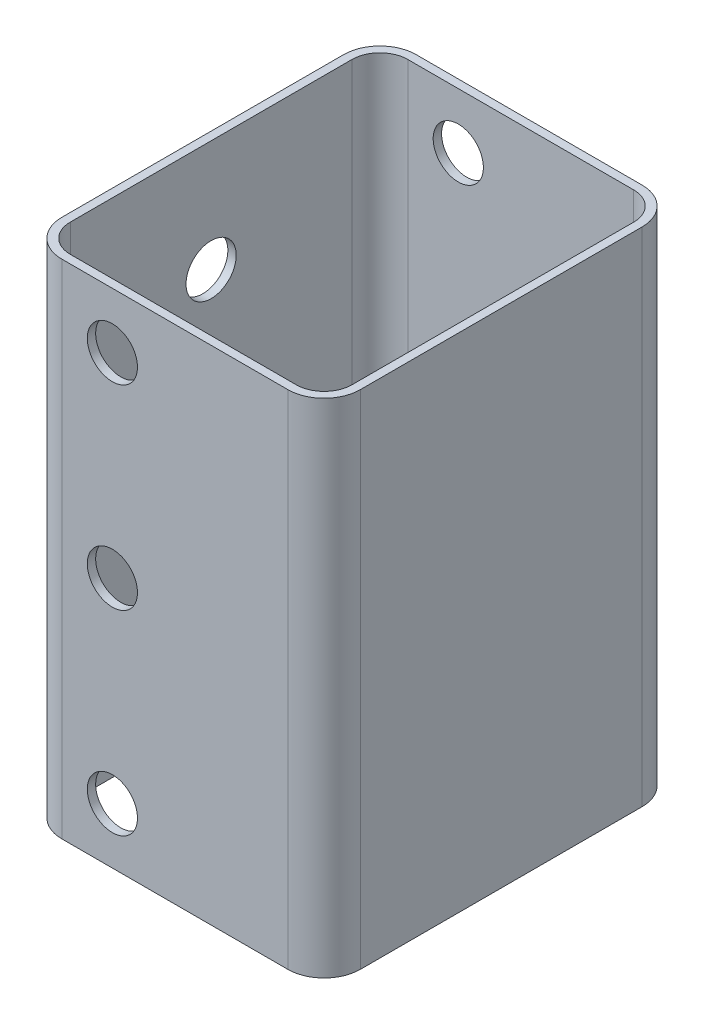
SolidWorks part; units mm, degrees
ref_plane "Front Plane" through (0, 0, 0) normal (0, 0, 1) x (1, 0, 0)
ref_plane "Top Plane" through (0, 0, 0) normal (0, 1, 0) x (1, 0, 0)
ref_plane "Right Plane" through (0, 0, 0) normal (1, 0, 0) x (0, 0, -1)
sketch "Sketch1" plane through (0, 0, 0) normal (0, 1, 0) x (1, 0, 0)
  line L0 (-20.25, -31.75) -> (20.25, -31.75)
  line L1 (-20.25, -30.25) -> (20.25, -30.25)
  line L2 (-25.25, -25.25) -> (-25.25, 25.25)
  line L3 (-20.25, 30.25) -> (20.25, 30.25)
  line L4 (25.25, -25.25) -> (25.25, 25.25)
  line L5 (-25.25, -30.25) -> (25.25, 30.25) construction
  line L6 (-25.25, 30.25) -> (25.25, -30.25) construction
  line L7 (26.75, -25.25) -> (26.75, 25.25)
  line L8 (-20.25, 31.75) -> (20.25, 31.75)
  line L9 (-26.75, -25.25) -> (-26.75, 25.25)
  arc A0 (20.25, 30.25) -> (25.25, 25.25) centre (20.25, 25.25) cw
  arc A1 (20.25, -30.25) -> (25.25, -25.25) centre (20.25, -25.25) ccw
  arc A2 (-20.25, -30.25) -> (-25.25, -25.25) centre (-20.25, -25.25) cw
  arc A3 (-25.25, 25.25) -> (-20.25, 30.25) centre (-20.25, 25.25) cw
  arc A4 (20.25, -31.75) -> (26.75, -25.25) centre (20.25, -25.25) ccw
  arc A5 (20.25, 31.75) -> (26.75, 25.25) centre (20.25, 25.25) cw
  arc A6 (-26.75, 25.25) -> (-20.25, 31.75) centre (-20.25, 25.25) cw
  arc A7 (-20.25, -31.75) -> (-26.75, -25.25) centre (-20.25, -25.25) cw
  point P0 (0, 0)
  dimension "D1" = 5
  dimension "D2" = 50.5
  dimension "D3" = 40.5
  dimension "D4" = 1.5
extrude "Boss-Extrude1" add sketch "Sketch1" along normal blind 90
sketch "Sketch2" plane through (-34.75, 0, 0) normal (-1, 0, 0) x (0, 0, 1)
  line L0 (0, 90) -> (0, 0) construction
  line L1 (-25.25, 90) -> (25.25, 90) construction
  line L2 (-25.25, 0) -> (25.25, 0) construction
  circle A0 centre (0, 70) radius 4.5
  circle A1 centre (0, 20) radius 4.5
  point P10 (0, 45)
  dimension "D1" = 9
  dimension "D2" = 9
  dimension "D3" = 50
  dimension "D4" = 25
extrude "Cut-Extrude1" cut sketch "Sketch2" against normal blind 10
sketch "Sketch3" plane through (0, 0, 32.25) normal (0, 0, 1) x (1, 0, 0)
  line L0 (-11.2, 90) -> (-11.2, 0) construction
  line L1 (-27.75, 90) -> (27.75, 90) construction
  line L2 (-27.75, 0) -> (27.75, 0) construction
  circle A0 centre (-11.2, 80) radius 4.5
  circle A1 centre (-11.2, 10) radius 4.5
  circle A2 centre (-11.2, 45) radius 4.5
  point P14 (-18.75, 45)
  dimension "D2" = 9
  dimension "D1" = 15.55
  dimension "D3" = 70
  dimension "D4" = 35
extrude "Cut-Extrude2" cut sketch "Sketch3" against normal blind 95
